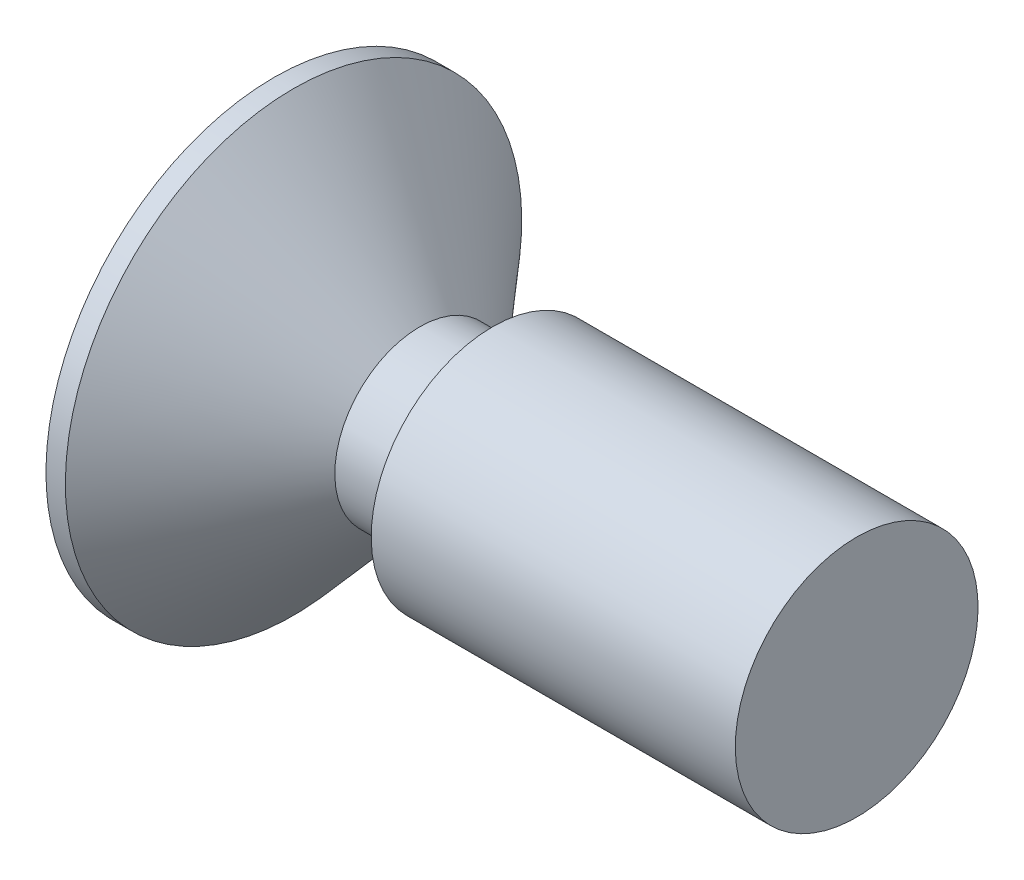
SolidWorks part; units mm, degrees
ref_plane "前视基准面" through (0, 0, 0) normal (0, 0, 1) x (1, 0, 0)
ref_plane "上视基准面" through (0, 0, 0) normal (0, 1, 0) x (1, 0, 0)
ref_plane "右视基准面" through (0, 0, 0) normal (1, 0, 0) x (0, 0, -1)
sketch "草图1" plane through (0, 0, 0) normal (0, 0, 1) x (1, 0, 0)
  line L0 (0, 0) -> (-43.2705, 0) construction
  line L1 (0, 0) -> (0, 1.25)
  line L2 (0, 1.25) -> (-3.75, 1.25)
  line L3 (-3.75, 1.25) -> (-3.75, 0.875)
  line L4 (-3.75, 0.875) -> (-4.5, 0.875)
  line L5 (-4.5, 0.875) -> (-5.8, 2.35)
  line L6 (-5.8, 2.35) -> (-6, 2.35)
  line L7 (-6, 2.35) -> (-6, 0)
  line L8 (-6, 0) -> (0, 0)
  dimension "D1" = 2.5
  dimension "D2" = 1.5
  dimension "D3" = 0.2
  dimension "D4" = 4.7
  dimension "D5" = 0.375
  dimension "D6" = 0.75
  dimension "D7" = 6
revolve "旋转1" add sketch "草图1" angle 360 about L0
cosmetic thread "装饰螺纹线1" parameters "D2"=2.15
sketch "草图2" plane through (-6, 0, 0) normal (-1, 0, 0) x (0, 0, 1)
  line L0 (1.5, 0) -> (-1.5, 0) construction
  line L1 (-0.3125, 1.5) -> (0.3125, 1.5)
  line L2 (-0.3125, 1.5) -> (-0.3125, 0.5625)
  line L3 (-0.3125, -1.5) -> (0.3125, -1.5)
  line L4 (0.3125, 1.5) -> (0.3125, 0.5625)
  line L5 (-1.5, 0.3125) -> (-0.5625, 0.3125)
  line L6 (-1.5, 0.3125) -> (-1.5, -0.3125)
  line L7 (-1.5, -0.3125) -> (-0.5625, -0.3125)
  line L8 (1.5, 0.3125) -> (1.5, -0.3125)
  line L9 (0, 1.5) -> (0, -1.5) construction
  line L10 (-0.3125, -0.5625) -> (-0.3125, -1.5)
  line L11 (0.5625, 0.3125) -> (1.5, 0.3125)
  line L12 (0.3125, -0.5625) -> (0.3125, -1.5)
  line L13 (0.5625, -0.3125) -> (1.5, -0.3125)
  arc A0 (-0.3125, -0.5625) -> (-0.5625, -0.3125) centre (-0.5625, -0.5625) ccw
  arc A1 (0.3125, -0.5625) -> (0.5625, -0.3125) centre (0.5625, -0.5625) cw
  arc A2 (0.5625, 0.3125) -> (0.3125, 0.5625) centre (0.5625, 0.5625) cw
  arc A3 (-0.3125, 0.5625) -> (-0.5625, 0.3125) centre (-0.5625, 0.5625) cw
  dimension "D3" = 0.25
  dimension "D1" = 0.625
  dimension "D2" = 3
extrude "切除-拉伸1" cut sketch "草图2" against normal blind 0.75
